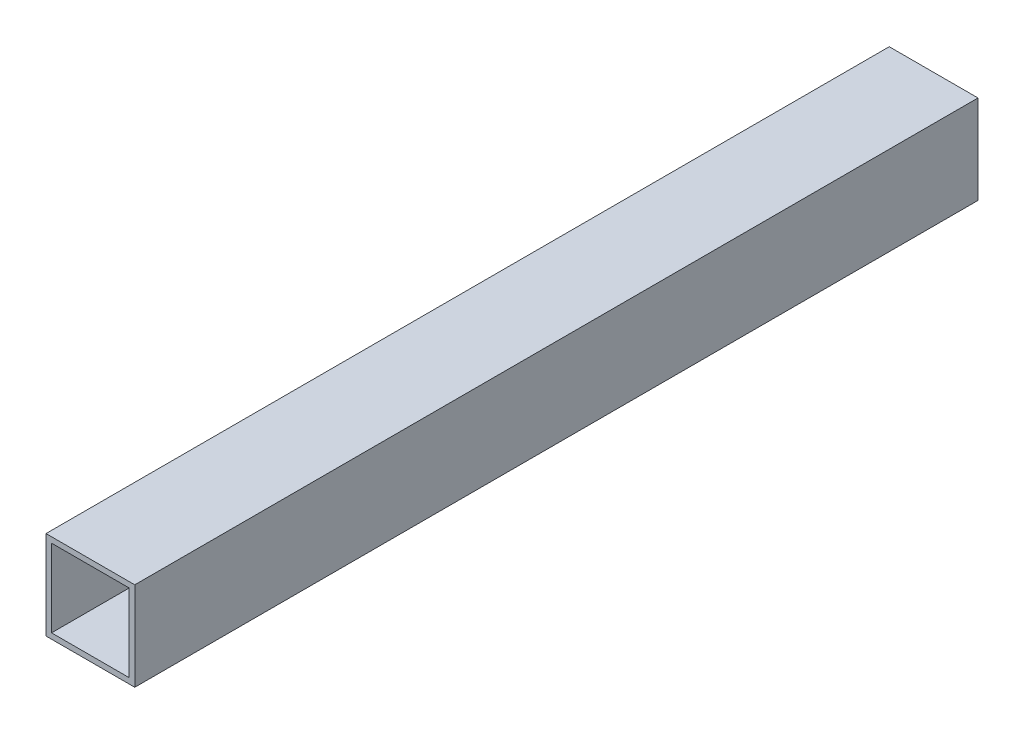
SolidWorks part; units mm, degrees
ref_plane "Front Plane" through (0, 0, 0) normal (0, 0, 1) x (1, 0, 0)
ref_plane "Top Plane" through (0, 0, 0) normal (0, 1, 0) x (1, 0, 0)
ref_plane "Right Plane" through (0, 0, 0) normal (1, 0, 0) x (0, 0, -1)
sketch "Sketch1" plane through (0, 0, 0) normal (0, 0, 1) x (1, 0, 0)
  line L1 (0, 0) -> (50.8, 0)
  line L2 (0, 0) -> (0, 50.8)
  line L3 (0, 50.8) -> (50.8, 50.8)
  line L4 (50.8, 0) -> (50.8, 50.8)
  line L5 (3.175, 47.625) -> (47.625, 47.625)
  line L6 (3.175, 47.625) -> (3.175, 3.175)
  line L7 (3.175, 3.175) -> (47.625, 3.175)
  line L8 (47.625, 47.625) -> (47.625, 3.175)
  dimension "D1" = 50.8
  dimension "D2" = 50.8
  dimension "D3" = 3.175
  dimension "D4" = 3.175
  dimension "D5" = 3.175
  dimension "D6" = 3.175
extrude "Boss-Extrude1" add sketch "Sketch1" along normal blind 482.6
